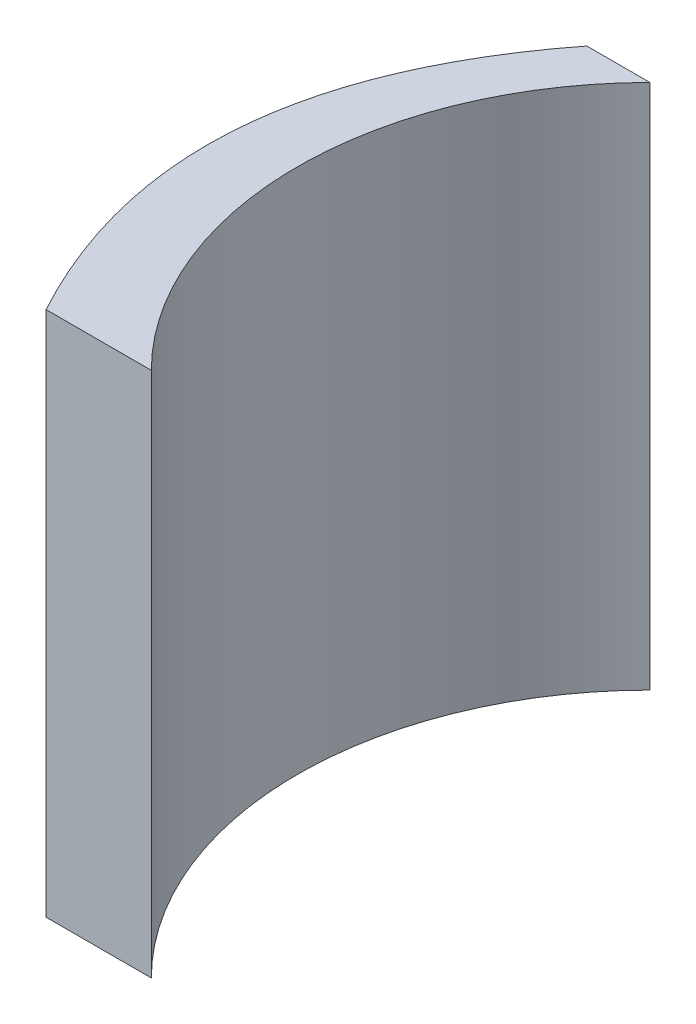
SolidWorks part; units mm, degrees
ref_plane "Front Plane" through (0, 0, 0) normal (0, 0, 1) x (1, 0, 0)
ref_plane "Top Plane" through (0, 0, 0) normal (0, 1, 0) x (1, 0, 0)
ref_plane "Right Plane" through (0, 0, 0) normal (1, 0, 0) x (0, 0, -1)
sketch "Sketch2" plane through (0, 0, 0) normal (0, 1, 0) x (1, 0, 0)
  line L0 (0, 0) -> (-23.6881, 23.6881) construction
  line L1 (0, 0) -> (-23.6881, -23.6881) construction
  line L2 (-23.6881, 23.6881) -> (-29.6881, 23.6881)
  line L3 (-23.6881, -23.6881) -> (-33.6881, -23.6881)
  line L4 (-33.5, 0) -> (-39.5, 0) construction
  line L5 (0, 33.5) -> (0, -33.5) construction
  line L6 (33.5, 0) -> (39.5, 0) construction
  circle A0 centre (0, 0) radius 33.5
  spline S0 degree 2 poles (-29.6881, 23.6881) (-47.2217, 1.1836) (-33.6881, -23.6881) knots 0 0 0 1 1 1
  dimension "D1" = 67
  dimension "D2" = 6
  dimension "D3" = 6
  dimension "D4" = 10
extrude "Boss-Extrude1" add sketch "Sketch2" along normal blind 50
sketch "Sketch3" plane through (0, 0, 23.6881) normal (0, 0, 1) x (1, 0, 0)
  line L1 (-33.6881, 17.5) -> (-41.6881, 17.5)
  line L2 (-33.6881, 17.5) -> (-33.6881, 7.5)
  line L3 (-33.6881, 7.5) -> (-41.6881, 7.5)
  line L4 (-41.6881, 17.5) -> (-41.6881, 7.5)
  line L5 (-23.6881, 0) -> (-33.6881, 0) construction
  line L6 (-23.6881, 50) -> (-23.6881, 0) construction
  dimension "D2" = 7.5
  dimension "D3" = 10
  dimension "D4" = 8
extrude "Cut-Extrude5" cut sketch "Sketch3" against normal blind 18
